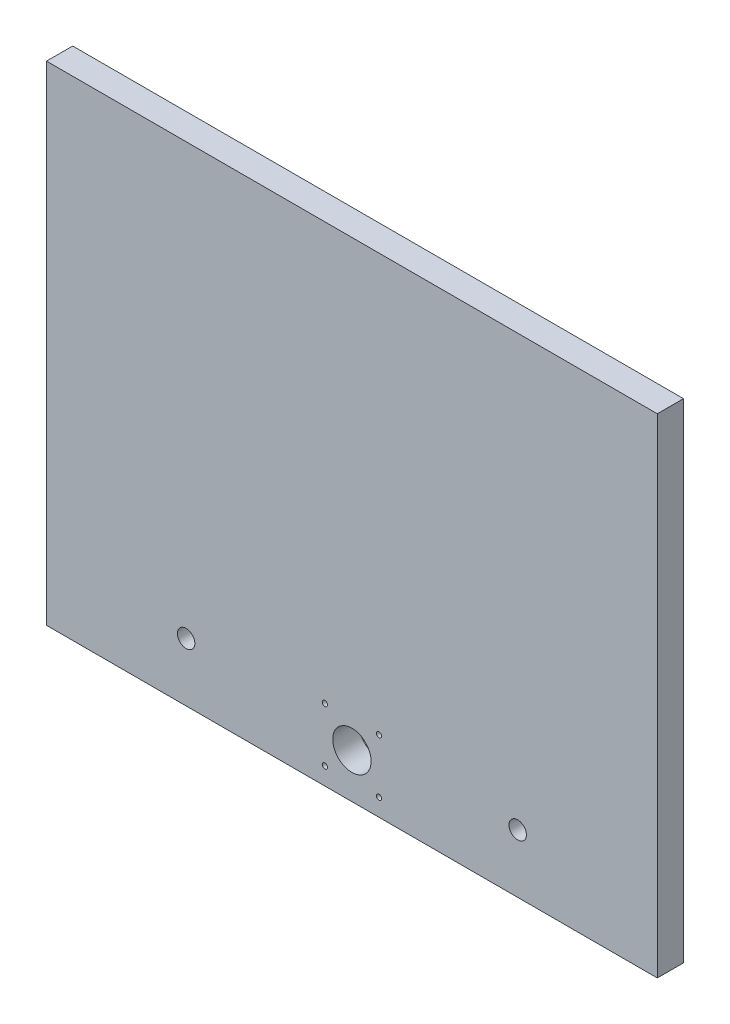
SolidWorks part; units mm, degrees
material "Balsa"
ref_plane "Front Plane" through (0, 0, 0) normal (0, 0, 1) x (1, 0, 0)
ref_plane "Top Plane" through (0, 0, 0) normal (0, 1, 0) x (1, 0, 0)
ref_plane "Right Plane" through (0, 0, 0) normal (1, 0, 0) x (0, 0, -1)
sketch "Sketch3" plane through (0, 0, 0) normal (0, 0, 1) x (1, 0, 0)
  line L1 (194.9189, 71.6975) -> (544.9189, 71.6975)
  line L2 (194.9189, 71.6975) -> (194.9189, 351.6975)
  line L3 (194.9189, 351.6975) -> (544.9189, 351.6975)
  line L4 (544.9189, 71.6975) -> (544.9189, 351.6975)
  circle A0 centre (354.4189, 112.6975) radius 1.5
  circle A1 centre (385.4189, 112.6975) radius 1.5
  circle A2 centre (354.4189, 81.6975) radius 1.5
  circle A3 centre (385.4189, 81.6975) radius 1.5
  circle A4 centre (369.9189, 97.1975) radius 11
  circle A5 centre (274.9189, 105.1975) radius 5
  circle A6 centre (464.9189, 105.1975) radius 5
  dimension "D3" = 31
  dimension "D7" = 22
  dimension "D1" = 280
  dimension "D2" = 350
  dimension "D4" = 31
  dimension "D5" = 10
  dimension "D6" = 159.5
  dimension "D8" = 175
  dimension "D9" = 25.5
other "AlignGroup1"
extrude "Boss-Extrude3" add sketch "Sketch3" along normal blind 15
